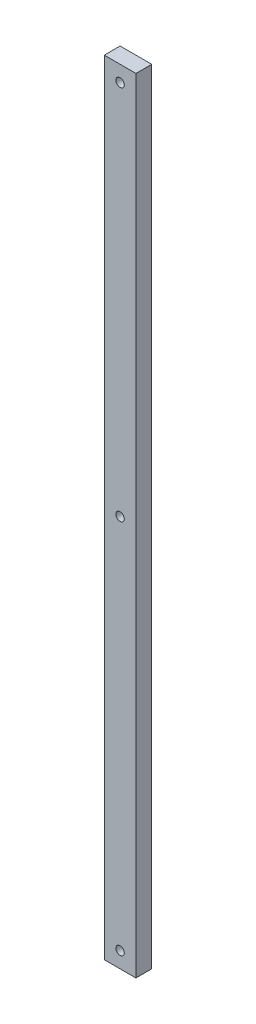
SolidWorks part; units mm, degrees
material "PE High Density"
ref_plane "Front Plane" through (0, 0, 0) normal (0, 0, 1) x (1, 0, 0)
ref_plane "Top Plane" through (0, 0, 0) normal (0, 1, 0) x (1, 0, 0)
ref_plane "Right Plane" through (0, 0, 0) normal (1, 0, 0) x (0, 0, -1)
sketch "Sketch1" plane through (0, 0, 0) normal (0, 0, 1) x (1, 0, 0)
  line L1 (0, 0) -> (-25.4, 0)
  line L2 (0, 0) -> (0, 628.65)
  line L3 (0, 628.65) -> (-25.4, 628.65)
  line L4 (-25.4, 0) -> (-25.4, 628.65)
  dimension "D1" = 25.4
  dimension "D2" = 628.65
extrude "Boss-Extrude1" add sketch "Sketch1" along normal blind 12.7
sketch "Sketch2" plane through (0, 0, 12.7) normal (0, 0, 1) x (1, 0, 0)
  line L0 (-25.4, 628.65) -> (-25.4, 0) construction
  line L1 (-25.4, 0) -> (0, 0) construction
  circle A0 centre (-12.7, 12.7) radius 3.3655
  dimension "D1" = 6.731
  dimension "D2" = 12.7
  dimension "D3" = 12.7
extrude "Cut-Extrude1" cut sketch "Sketch2" against normal through all
pattern_linear "LPattern1" count 3 spacing 301.625 along (0, 1, 0) of "Cut-Extrude1"
